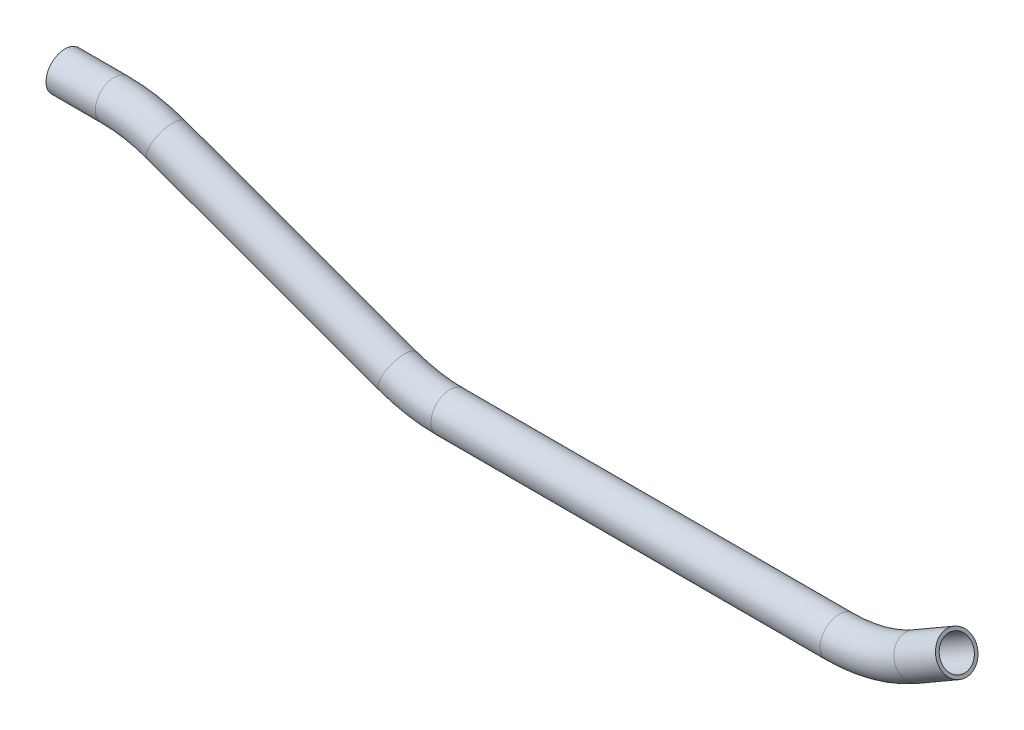
SolidWorks part; units mm, degrees
ref_plane "Front Plane" through (0, 0, 0) normal (0, 0, 1) x (1, 0, 0)
ref_plane "Top Plane" through (0, 0, 0) normal (0, 1, 0) x (1, 0, 0)
ref_plane "Right Plane" through (0, 0, 0) normal (1, 0, 0) x (0, 0, -1)
sketch "Sketch1" plane through (0, 0, 0) normal (0, 0, 1) x (1, 0, 0)
  line L0 (-82.7154, 8.1252) -> (-58.0516, 8.1252)
  line L1 (-31.9896, 3.5298) -> (83.8823, -38.6442)
  line L2 (109.9443, -43.2396) -> (304.6904, -43.2396)
  line L3 (342.7904, -33.0307) -> (363.603, -21.0146)
  line L4 (-82.7154, 8.1252) -> (-31.1546, 8.1252) construction
  line L5 (83.8823, -38.6442) -> (-31.9896, 3.5298) construction
  line L6 (-31.9896, 3.5298) -> (-170.3565, 53.8912) construction
  line L7 (-31.9896, 3.5298) -> (83.8823, -38.6442) construction
  line L8 (83.8823, -38.6442) -> (11.9374, -12.4584) construction
  line L9 (304.6904, -43.2396) -> (109.9443, -43.2396) construction
  line L10 (109.9443, -43.2396) -> (147.0367, -43.2396) construction
  line L11 (109.9443, -43.2396) -> (304.6904, -43.2396) construction
  line L12 (363.603, -21.0146) -> (342.7904, -33.0307) construction
  line L13 (109.9443, -43.2396) -> (304.6904, -43.2396) construction
  line L14 (304.6904, -43.2396) -> (408.8691, -43.2396) construction
  line L16 (342.7904, -33.0307) -> (268.3238, -76.0241) construction
  arc A0 (-58.0516, 8.1252) -> (-31.9896, 3.5298) centre (-58.0516, -68.0748) cw
  arc A1 (83.8823, -38.6442) -> (109.9443, -43.2396) centre (109.9443, 32.9604) ccw
  arc A2 (304.6904, -43.2396) -> (342.7904, -33.0307) centre (304.6904, 32.9604) ccw
  point P10 (325.1082, -43.2396)
  point P18 (96.5082, -43.2396)
  point P19 (-44.6154, 8.1252)
  dimension "D3" = 76.2
  dimension "D6" = 76.2
  dimension "D9" = 228.6
  dimension "D8" = 44.45
  dimension "D10" = 76.2
  dimension "D1" = 38.1
  dimension "D2" = 20
  dimension "D4" = 150.1806
  dimension "D5" = 20
  dimension "D7" = 30
ref_plane "Plane1" through (-82.7154, 8.1252, 0) normal (1, 0, 0) x (0, 0, -1)
sketch "Sketch2" plane through (-82.7154, 8.1252, 0) normal (1, 0, 0) x (0, 0, -1)
  circle A0 centre (0, 0) radius 9.525
  circle A1 centre (0, 0) radius 7.874
  dimension "D1" = 15.748
  dimension "D2" = 19.05
sweep "Sweep1" add profiles "Sketch2" path "Sketch1"
